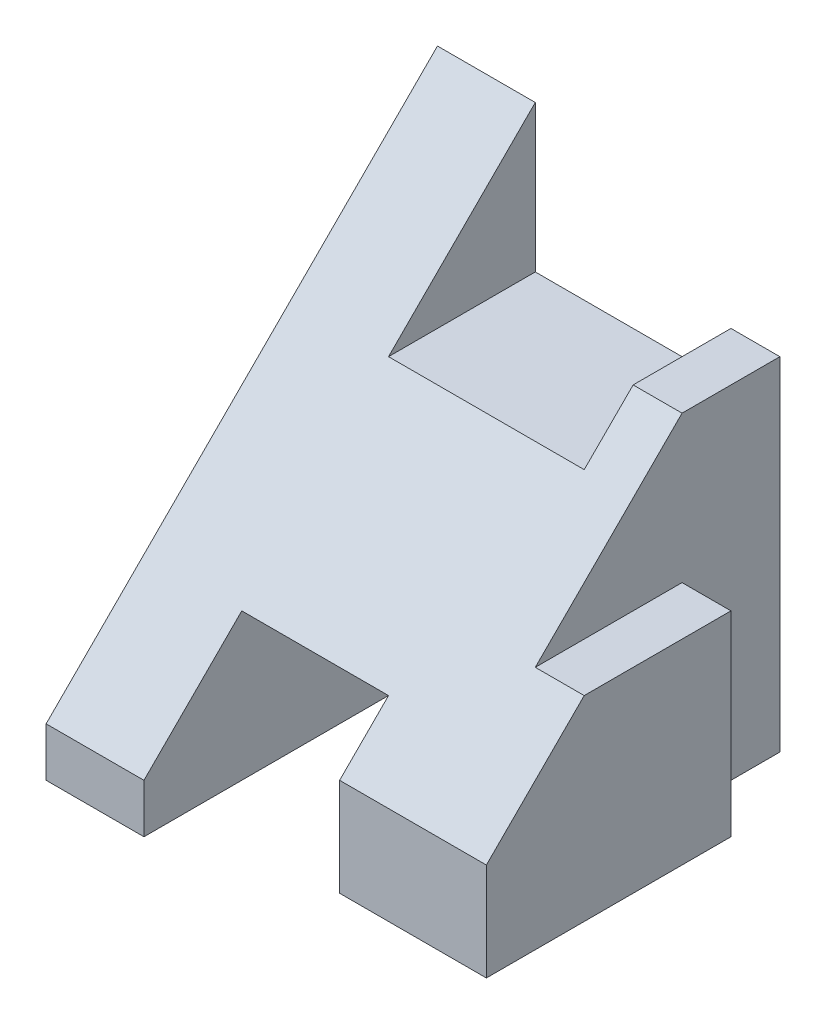
SolidWorks part; units mm, degrees
ref_plane "Front Plane" through (0, 0, 0) normal (0, 0, 1) x (1, 0, 0)
ref_plane "Top Plane" through (0, 0, 0) normal (0, 1, 0) x (1, 0, 0)
ref_plane "Right Plane" through (0, 0, 0) normal (1, 0, 0) x (0, 0, -1)
sketch "Sketch1" plane through (0, 0, 0) normal (0, 0, 1) x (1, 0, 0)
  line L1 (4, -4.5) -> (-4, -4.5)
  line L2 (4, -4.5) -> (4, 4.5)
  line L3 (4, 4.5) -> (-4, 4.5)
  line L4 (-4, -4.5) -> (-4, 4.5)
  line L5 (4, -4.5) -> (-4, 4.5) construction
  line L6 (4, 4.5) -> (-4, -4.5) construction
  point P0 (0, 0)
  dimension "D1" = 8
  dimension "D2" = 9
extrude "Boss-Extrude1" add sketch "Sketch1" along normal blind 8
sketch "Sketch2" plane through (0, 4.5, 0) normal (0, 1, 0) x (1, 0, 0)
  line L0 (-2, 0) -> (-2, -3)
  line L1 (4, 0) -> (-4, 0) construction
  line L2 (-2, -3) -> (2, -3)
  line L3 (2, -3) -> (2, 0)
  line L4 (2, 0) -> (-2, 0)
  dimension "D1" = 2
  dimension "D2" = 2
  dimension "D3" = 3
extrude "Cut-Extrude1" cut sketch "Sketch2" against normal blind 3
sketch "Sketch3" plane through (0, 4.5, 0) normal (0, 1, 0) x (1, 0, 0)
  line L0 (4, 0) -> (2, 0)
  line L1 (4, 0) -> (2, 0) construction
  line L2 (2, 0) -> (2, -2)
  line L3 (2, -3) -> (2, 0) construction
  line L4 (2, -2) -> (4, -2)
  line L5 (4, -8) -> (4, 0) construction
  line L6 (4, -2) -> (4, 0)
  dimension "D1" = 2
  dimension "D2" = 2
extrude "Cut-Extrude2" cut sketch "Sketch3" against normal blind 2
sketch "Sketch4" plane through (4, 0, 0) normal (1, 0, 0) x (0, 0, -1)
  line L0 (0, -4.5) -> (0, 2.5)
  line L1 (0, 2.5) -> (-2, 2.5)
  line L2 (-2, 2.5) -> (-5, -0.5)
  line L3 (-5, -0.5) -> (-2, -0.5)
  line L4 (-2, -0.5) -> (-2, -4.5)
  line L5 (-8, -4.5) -> (0, -4.5) construction
  line L6 (-2, -4.5) -> (0, -4.5)
  dimension "D1" = 2
  dimension "D2" = 3
  dimension "D3" = 4
extrude "Cut-Extrude3" cut sketch "Sketch4" against normal blind 1
sketch "Sketch5" plane through (4, 0, 0) normal (1, 0, 0) x (0, 0, -1)
  line L0 (0, 4.5) -> (-8, -3.5)
  line L1 (-8, -4.5) -> (-8, 4.5) construction
  line L2 (-8, -3.5) -> (-8, 4.5)
  line L3 (-8, 4.5) -> (0, 4.5)
  dimension "D1" = 1
extrude "Cut-Extrude4" cut sketch "Sketch5" against normal through all
sketch "Sketch6" plane through (0, 0, 0) normal (0, 0, -1) x (-1, 0, 0)
  line L0 (-1, -4.5) -> (-1, -1.5)
  line L1 (4, -4.5) -> (-3, -4.5) construction
  line L2 (-1, -1.5) -> (2, -1.5)
  line L3 (2, -1.5) -> (2, -4.5)
  line L4 (2, -4.5) -> (-1, -4.5)
  dimension "D1" = 2
  dimension "D2" = 2
  dimension "D3" = 3
extrude "Cut-Extrude5" cut sketch "Sketch6" against normal through all
sketch "Sketch7" plane through (0, -4.5, 0) normal (0, -1, 0) x (1, 0, 0)
  line L0 (4, 8) -> (1, 8)
  line L1 (1, 8) -> (1, 7)
  line L2 (1, 8) -> (1, 0) construction
  line L3 (1, 7) -> (4, 7)
  line L4 (4, 8) -> (4, 2) construction
  line L5 (4, 7) -> (4, 8)
  dimension "D1" = 1
extrude "Cut-Extrude6" cut sketch "Sketch7" against normal blind 2
